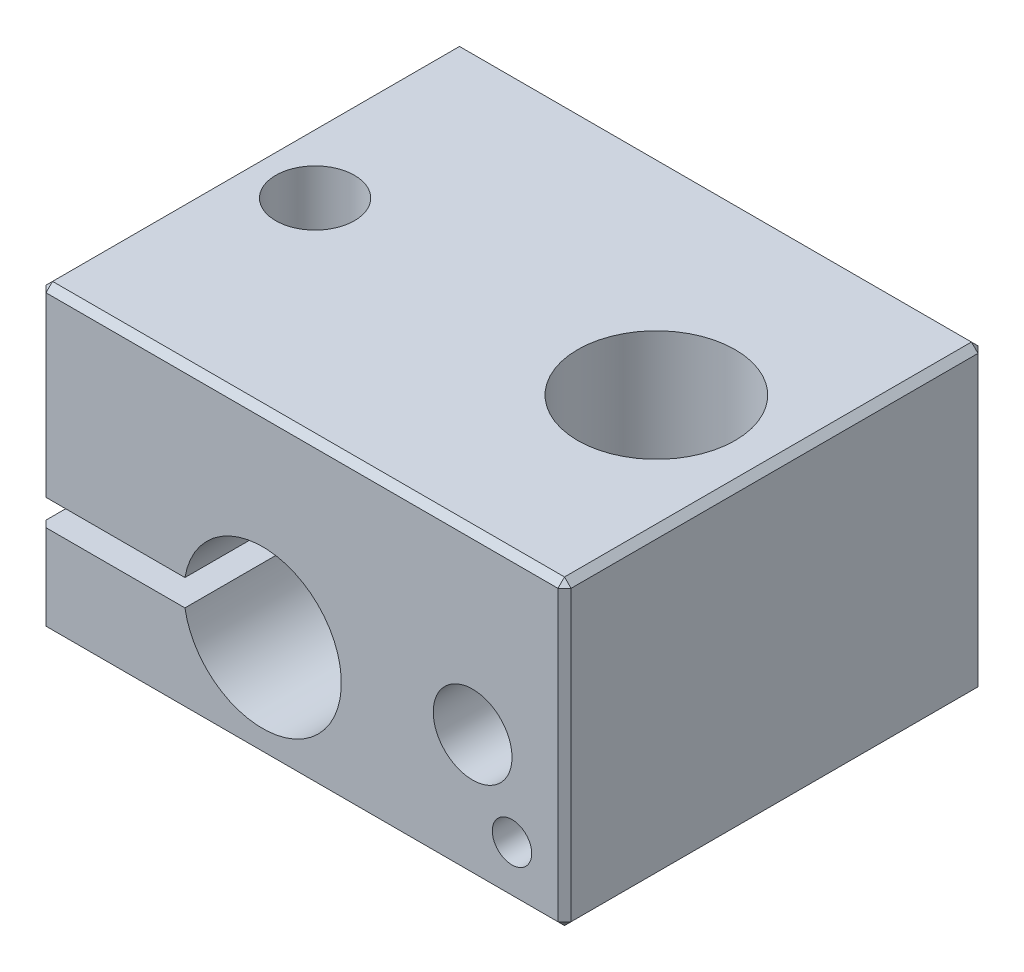
SolidWorks part; units mm, degrees
material "1060 Alloy"
ref_plane "Front Plane" through (0, 0, 0) normal (0, 0, 1) x (1, 0, 0)
ref_plane "Top Plane" through (0, 0, 0) normal (0, 1, 0) x (1, 0, 0)
ref_plane "Right Plane" through (0, 0, 0) normal (1, 0, 0) x (0, 0, -1)
ref_plane "Plane1" through (0, 0, 0) normal (0, -1, 0) x (1, 0, 0)
sketch "Sketch1" plane through (0, 0, 0) normal (0, -1, 0) x (1, 0, 0)
  line L0 (10, -8) -> (10, 8)
  line L1 (10, 8) -> (-10, 8)
  line L2 (-10, 8) -> (-10, -8)
  line L3 (-10, -8) -> (10, -8)
extrude "Boss-Extrude1" add sketch "Sketch1" against normal blind 11.5
sketch "Sketch2" plane through (0, 0, -8) normal (0, 0, -1) x (-1, 0, 0)
  line L0 (10, 3.5) -> (10, 4.5)
  line L1 (10, 4.5) -> (4.458, 4.5)
  line L2 (4.458, 3.5) -> (10, 3.5)
  arc A0 (4.458, 4.5) -> (4.458, 3.5) centre (1.5, 4) cw
extrude "Cut-Extrude1" cut sketch "Sketch2" against normal through all
ref_plane "Plane2" through (0, 4, 0) normal (0, 1, 0) x (1, 0, 0)
sketch "Sketch3" plane through (0, 4, 0) normal (0, 1, 0) x (1, 0, 0)
  line L0 (1.5, 8) -> (-1.5, 8)
  line L1 (-1.5, 8) -> (-1.5, -8)
  line L2 (-1.5, -8) -> (1.5, -8)
  line L3 (1.5, -8) -> (1.5, 8)
  line L4 (-1.5, 8) -> (-1.5, -8) construction
revolve "Cut-Revolve1" cut sketch "Sketch3" angle 360 about L4
hole_wizard "Ø3.0 (3) Diameter Hole1" positions "Sketch5" profile "Sketch4" hole size "Ø3.0" standard "ANSI Metric"
sketch "Sketch5" plane through (0, 4.5, 0) normal (0, -1, 0) x (-1, 0, 0)
  point P0 (7.5, 0)
sketch "Sketch4" plane through (-7.5, 4.5, 0) normal (1, 0, 0) x (0, 0, -1)
  line L0 (0, 0) -> (0, 7)
  line L1 (0, 7) -> (1.5, 7)
  line L2 (1.5, 7) -> (1.5, 0)
  line L5 (1.5, 0) -> (0, 0)
  line L11 (0, -6.35) -> (0, 107.95) construction
  dimension "Thru Hole Dia." = 3
  dimension "Thru Hole Depth" = 7
hole_wizard "Ø6.0 (6) Diameter Hole1" positions "Sketch7" profile "Sketch6" hole size "Ø6.0" standard "ANSI Metric"
sketch "Sketch7" plane through (0, 0, 0) normal (0, -1, 0) x (-1, 0, 0)
  point P0 (-5.5, 0)
sketch "Sketch6" plane through (5.5, 0, 0) normal (1, 0, 0) x (0, 0, -1)
  line L0 (0, 0) -> (0, 11.5)
  line L1 (0, 11.5) -> (3, 11.5)
  line L2 (3, 11.5) -> (3, 0)
  line L5 (3, 0) -> (0, 0)
  line L11 (0, -6.35) -> (0, 107.95) construction
  dimension "Thru Hole Dia." = 6
  dimension "Thru Hole Depth" = 11.5
hole_wizard "Ø3.0 (3) Diameter Hole2" positions "Sketch9" profile "Sketch8" hole size "Ø3.0" standard "ANSI Metric"
sketch "Sketch9" plane through (0, 3.5, 0) normal (0, 1, 0) x (1, 0, 0)
  point P0 (-7.5, 0)
sketch "Sketch8" plane through (-7.5, 3.5, 0) normal (1, 0, 0) x (0, 0, 1)
  line L0 (0, 0) -> (0, 3.5)
  line L1 (0, 3.5) -> (1.5, 3.5)
  line L2 (1.5, 3.5) -> (1.5, 0)
  line L5 (1.5, 0) -> (0, 0)
  line L11 (0, -6.35) -> (0, 107.95) construction
  dimension "Thru Hole Dia." = 3
  dimension "Thru Hole Depth" = 3.5
hole_wizard "Ø3.0 (3) Diameter Hole3" positions "Sketch11" profile "Sketch10" hole size "Ø3.0" standard "ANSI Metric"
sketch "Sketch11" plane through (0, 0, 8) normal (0, 0, 1) x (1, 0, 0)
  point P0 (6.5, 4.8)
sketch "Sketch10" plane through (6.5, 4.8, 8) normal (1, 0, 0) x (0, -1, 0)
  line L0 (0, 0) -> (0, 3.5)
  line L1 (0, 3.5) -> (1.5, 3.5)
  line L2 (1.5, 3.5) -> (1.5, 0)
  line L5 (1.5, 0) -> (0, 0)
  line L10 (0, 3.5) -> (-1.5, 3.5) construction
  line L11 (0, -6.35) -> (0, 107.95) construction
  dimension "Hole Dia." = 3
  dimension "Hole Depth" = 3.5
  dimension "Drill Angle" = 180
hole_wizard "Ø1.5 (1.5) Diameter Hole1" positions "Sketch13" profile "Sketch12" hole size "Ø1.5" standard "ANSI Metric"
sketch "Sketch13" plane through (0, 0, 8) normal (0, 0, 1) x (1, 0, 0)
  point P0 (8, 2)
sketch "Sketch12" plane through (8, 2, 8) normal (1, 0, 0) x (0, -1, 0)
  line L0 (0, 0) -> (0, 4.5)
  line L1 (0, 4.5) -> (0.75, 4.5)
  line L2 (0.75, 4.5) -> (0.75, 0)
  line L5 (0.75, 0) -> (0, 0)
  line L10 (0, 4.5) -> (-0.75, 4.5) construction
  line L11 (0, -6.35) -> (0, 107.95) construction
  dimension "Hole Dia." = 1.5
  dimension "Hole Depth" = 4.5
  dimension "Drill Angle" = 180
chamfer "Chamfer1" distance 0.25 angle 45 14 edges at (-10, 1.75, -8) (-10, 0, 0) (-10, 1.75, 8) (0, 0, -8) (0, 0, 8) (10, 0, 0) (-10, 8, -8) (-10, 11.5, 0) (-10, 8, 8) (10, 5.75, -8) (10, 5.75, 8) (0, 11.5, -8) (0, 11.5, 8) (10, 11.5, 0)
